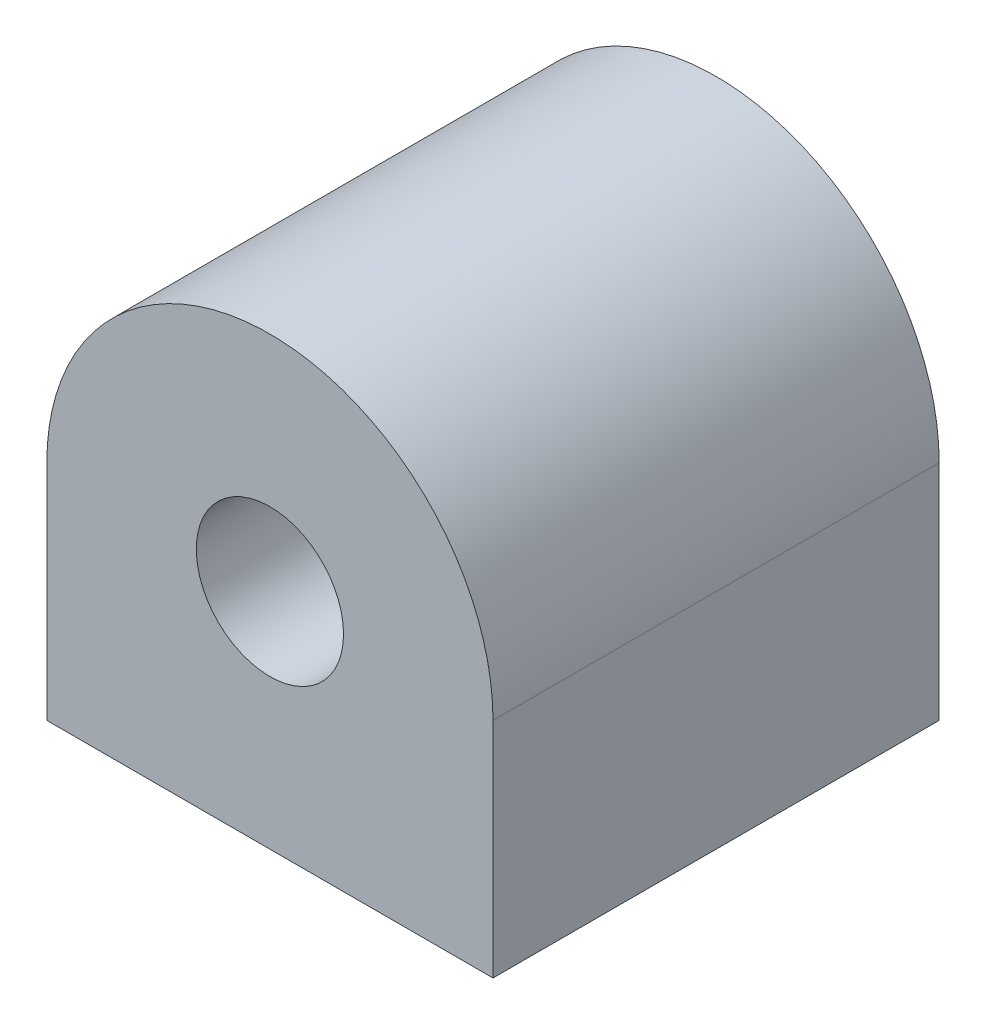
SolidWorks part; units mm, degrees
ref_plane "Front Plane" through (0, 0, 0) normal (0, 0, 1) x (1, 0, 0)
ref_plane "Top Plane" through (0, 0, 0) normal (0, 1, 0) x (1, 0, 0)
ref_plane "Right Plane" through (0, 0, 0) normal (1, 0, 0) x (0, 0, -1)
sketch "Sketch1" plane through (0, 0, 0) normal (0, 0, 1) x (1, 0, 0)
  line L0 (5, 0) -> (5, -5)
  line L2 (5, -5) -> (-5, -5)
  line L3 (-5, 0) -> (-5, -5)
  arc A0 (-5, 0) -> (5, 0) centre (0, 0) cw
  circle A1 centre (0, 0) radius 1.65
  dimension "D1" = 5
  dimension "D2" = 10
extrude "Boss-Extrude1" add sketch "Sketch1" along normal blind 10
